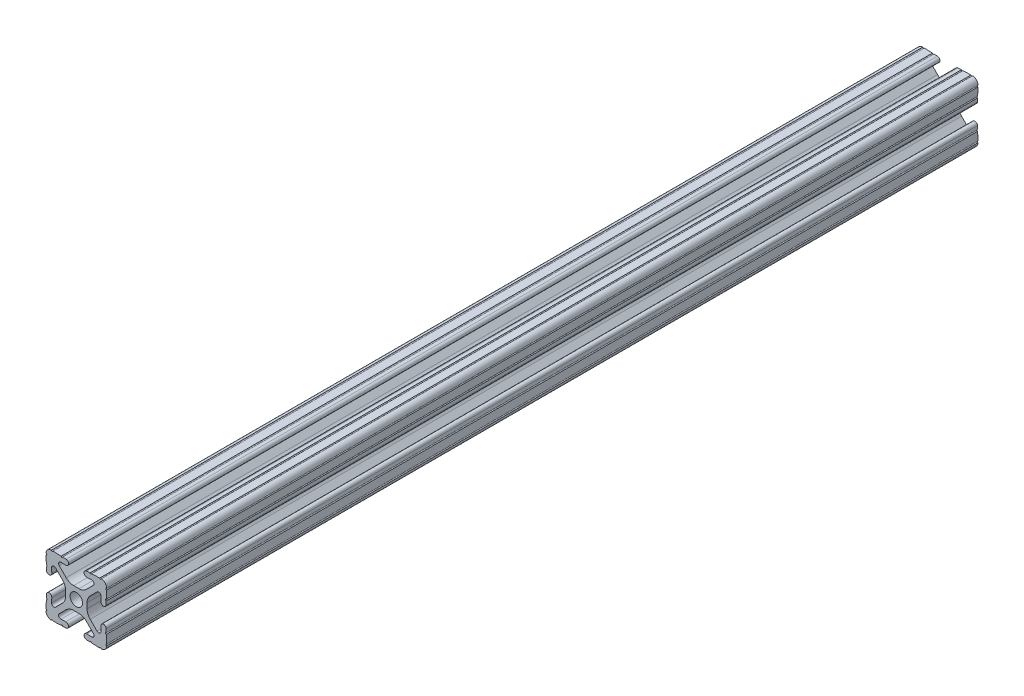
SolidWorks part; units mm, degrees
ref_plane "Front Plane" through (0, 0, 0) normal (0, 0, 1) x (1, 0, 0)
ref_plane "Top Plane" through (0, 0, 0) normal (0, 1, 0) x (1, 0, 0)
ref_plane "Right Plane" through (0, 0, 0) normal (1, 0, 0) x (0, 0, -1)
sketch "Sketch1" plane through (0, 0, 0) normal (0, 0, 1) x (1, 0, 0)
  line L0 (0, 12.7) -> (-12.7814, 12.7) construction
  line L1 (-4.5085, 0) -> (-4.5085, 2.9459)
  line L2 (-6.0437, 12.5461) -> (-10.0976, 12.6876) construction
  line L3 (-11.5616, 12.4229) -> (-4.3159, 12.1699) construction
  line L4 (-6.4364, 10.3486) -> (-6.3592, 12.5571) construction
  line L6 (-2.9459, 4.5085) -> (0, 4.5085)
  line L7 (0, 0) -> (0, 12.7) construction
  line L8 (0, 0) -> (-12.7814, 0) construction
  line L9 (0.7813, 0.7813) -> (-0.7813, -0.7813) construction
  line L10 (-2.9459, 4.5085) -> (-7.1484, 8.711)
  line L11 (-4.5085, 2.9459) -> (-8.711, 7.1484)
  line L13 (0, 0) -> (-12.7814, 12.7814) construction
  line L14 (-10.4131, 12.6987) -> (-4.3048, 12.4853)
  line L15 (-4.3048, 12.4853) -> (-4.382, 10.2769) construction
  line L16 (-4.382, 10.2769) -> (-6.4364, 10.3486)
  line L17 (-12.6987, 10.4131) -> (-12.4853, 4.3048)
  line L18 (-10.2769, 4.382) -> (-10.3486, 6.4364)
  circle A0 centre (0, 0) radius 2.6035
  arc A1 (-4.382, 10.2769) -> (-4.3048, 12.4853) centre (-4.3434, 11.3811) ccw
  arc A2 (-7.1484, 8.711) -> (-6.4364, 10.3486) centre (-6.4698, 9.3896) cw
  arc A3 (-8.711, 7.1484) -> (-10.3486, 6.4364) centre (-9.3896, 6.4698) ccw
  arc A4 (-10.2769, 4.382) -> (-12.4853, 4.3048) centre (-11.3811, 4.3434) cw
  arc A5 (-10.4131, 12.6987) -> (-12.6987, 10.4131) centre (-10.4902, 10.4902) ccw
  arc A6 (-10.4131, 12.6987) -> (-9.7821, 12.6766) centre (-10.0976, 12.6876) ccw
  arc A7 (-6.3592, 12.5571) -> (-5.7282, 12.5351) centre (-6.0437, 12.5461) ccw
  arc A8 (-12.5571, 6.3592) -> (-12.5351, 5.7282) centre (-12.5461, 6.0437) cw
  arc A9 (-12.6987, 10.4131) -> (-12.6766, 9.7821) centre (-12.6876, 10.0976) cw
  dimension "D1" = 5.207
  dimension "D5" = 14.859
  dimension "D9" = 2
  dimension "D2" = 25.4
  dimension "D12" = 0.6314
  dimension "D10" = 2.2098
  dimension "D3" = 9.017
  dimension "D4" = 9.017
  dimension "D6" = 25.4
  dimension "D7" = 6.477
  dimension "D8" = 2.2098
  dimension "D11" = 12.7
sketch "Sketch3" plane through (0, 0, 0) normal (0, 0, 1) x (1, 0, 0)
  line L0 (-2.9459, 4.5085) -> (0, 4.5085) construction
  line L1 (-2.9459, 4.5085) -> (-7.1484, 8.711) construction
  line L2 (-4.382, 10.2769) -> (-6.4364, 10.3486) construction
  line L3 (-10.4131, 12.6987) -> (-4.3048, 12.4853) construction
  line L4 (-4.5085, 0) -> (-4.5085, 2.9459) construction
  line L5 (-4.5085, 2.9459) -> (-8.711, 7.1484) construction
  line L6 (-10.2769, 4.382) -> (-10.3486, 6.4364) construction
  line L7 (-12.6987, 10.4131) -> (-12.4853, 4.3048) construction
  line L8 (-1.1153, 4.5085) -> (1.1153, 4.5085)
  line L9 (-4.2404, 5.803) -> (-7.1484, 8.711)
  line L10 (-4.382, 10.2769) -> (-6.4364, 10.3486)
  line L11 (-9.7821, 12.6766) -> (-6.3592, 12.5571)
  line L12 (-4.5085, -1.1153) -> (-4.5085, 1.1153)
  line L13 (-5.803, 4.2404) -> (-8.711, 7.1484)
  line L14 (-10.2769, 4.382) -> (-10.3486, 6.4364)
  line L15 (-12.6766, 9.7821) -> (-12.5571, 6.3592)
  line L16 (-5.7282, 12.5351) -> (-4.3048, 12.4853)
  line L17 (-12.5351, 5.7282) -> (-12.4853, 4.3048)
  line L18 (0, 0) -> (0, 12.7) construction
  line L19 (0, 0) -> (-12.7814, 0) construction
  line L20 (12.5351, 5.7282) -> (12.4853, 4.3048)
  line L21 (5.7282, 12.5351) -> (4.3048, 12.4853)
  line L22 (12.6766, 9.7821) -> (12.5571, 6.3592)
  line L23 (10.2769, 4.382) -> (10.3486, 6.4364)
  line L24 (5.803, 4.2404) -> (8.711, 7.1484)
  line L25 (4.5085, -1.1153) -> (4.5085, 1.1153)
  line L26 (9.7821, 12.6766) -> (6.3592, 12.5571)
  line L27 (4.382, 10.2769) -> (6.4364, 10.3486)
  line L28 (4.2404, 5.803) -> (7.1484, 8.711)
  line L29 (4.2404, -5.803) -> (7.1484, -8.711)
  line L30 (4.382, -10.2769) -> (6.4364, -10.3486)
  line L31 (9.7821, -12.6766) -> (6.3592, -12.5571)
  line L32 (5.803, -4.2404) -> (8.711, -7.1484)
  line L33 (10.2769, -4.382) -> (10.3486, -6.4364)
  line L34 (12.6766, -9.7821) -> (12.5571, -6.3592)
  line L35 (5.7282, -12.5351) -> (4.3048, -12.4853)
  line L36 (12.5351, -5.7282) -> (12.4853, -4.3048)
  line L37 (-12.5351, -5.7282) -> (-12.4853, -4.3048)
  line L38 (-5.7282, -12.5351) -> (-4.3048, -12.4853)
  line L39 (-12.6766, -9.7821) -> (-12.5571, -6.3592)
  line L40 (-10.2769, -4.382) -> (-10.3486, -6.4364)
  line L41 (-5.803, -4.2404) -> (-8.711, -7.1484)
  line L42 (-9.7821, -12.6766) -> (-6.3592, -12.5571)
  line L43 (-4.382, -10.2769) -> (-6.4364, -10.3486)
  line L44 (-4.2404, -5.803) -> (-7.1484, -8.711)
  line L45 (-1.1153, -4.5085) -> (1.1153, -4.5085)
  arc A0 (-10.4131, 12.6987) -> (-9.7821, 12.6766) centre (-10.0976, 12.6876) ccw construction
  arc A1 (-6.4364, 10.3486) -> (-7.1484, 8.711) centre (-6.4698, 9.3896) ccw construction
  arc A2 (-4.382, 10.2769) -> (-4.3048, 12.4853) centre (-4.3434, 11.3811) ccw construction
  arc A3 (-8.711, 7.1484) -> (-10.3486, 6.4364) centre (-9.3896, 6.4698) ccw construction
  arc A4 (-12.4853, 4.3048) -> (-10.2769, 4.382) centre (-11.3811, 4.3434) ccw construction
  arc A5 (-6.3592, 12.5571) -> (-5.7282, 12.5351) centre (-6.0437, 12.5461) ccw construction
  arc A6 (-10.4131, 12.6987) -> (-12.6987, 10.4131) centre (-10.4902, 10.4902) ccw construction
  arc A7 (-12.6766, 9.7821) -> (-12.6987, 10.4131) centre (-12.6876, 10.0976) ccw construction
  arc A8 (-12.5351, 5.7282) -> (-12.5571, 6.3592) centre (-12.5461, 6.0437) ccw construction
  arc A9 (-10.4131, 12.6987) -> (-9.7821, 12.6766) centre (-10.0976, 12.6876) ccw
  arc A10 (-6.4364, 10.3486) -> (-7.1484, 8.711) centre (-6.4698, 9.3896) ccw
  arc A11 (-4.382, 10.2769) -> (-4.3048, 12.4853) centre (-4.3434, 11.3811) ccw
  arc A12 (-8.711, 7.1484) -> (-10.3486, 6.4364) centre (-9.3896, 6.4698) ccw
  arc A13 (-12.4853, 4.3048) -> (-10.2769, 4.382) centre (-11.3811, 4.3434) ccw
  arc A14 (-6.3592, 12.5571) -> (-5.7282, 12.5351) centre (-6.0437, 12.5461) ccw
  arc A15 (-10.4131, 12.6987) -> (-12.6987, 10.4131) centre (-10.4902, 10.4902) ccw
  arc A16 (-12.6766, 9.7821) -> (-12.6987, 10.4131) centre (-12.6876, 10.0976) ccw
  arc A17 (-12.5351, 5.7282) -> (-12.5571, 6.3592) centre (-12.5461, 6.0437) ccw
  arc A18 (-1.1153, 4.5085) -> (-4.2404, 5.803) centre (-1.1153, 8.9281) cw
  arc A19 (4.5085, 1.1153) -> (5.803, 4.2404) centre (8.9281, 1.1153) cw
  arc A20 (1.1153, 4.5085) -> (4.2404, 5.803) centre (1.1153, 8.9281) ccw
  arc A21 (-4.5085, 1.1153) -> (-5.803, 4.2404) centre (-8.9281, 1.1153) ccw
  arc A22 (12.5351, 5.7282) -> (12.5571, 6.3592) centre (12.5461, 6.0437) cw
  arc A23 (12.6766, 9.7821) -> (12.6987, 10.4131) centre (12.6876, 10.0976) cw
  arc A24 (10.4131, 12.6987) -> (12.6987, 10.4131) centre (10.4902, 10.4902) cw
  arc A25 (6.3592, 12.5571) -> (5.7282, 12.5351) centre (6.0437, 12.5461) cw
  arc A26 (12.4853, 4.3048) -> (10.2769, 4.382) centre (11.3811, 4.3434) cw
  arc A27 (8.711, 7.1484) -> (10.3486, 6.4364) centre (9.3896, 6.4698) cw
  arc A28 (4.382, 10.2769) -> (4.3048, 12.4853) centre (4.3434, 11.3811) cw
  arc A29 (6.4364, 10.3486) -> (7.1484, 8.711) centre (6.4698, 9.3896) cw
  arc A30 (10.4131, 12.6987) -> (9.7821, 12.6766) centre (10.0976, 12.6876) cw
  arc A31 (10.4131, -12.6987) -> (9.7821, -12.6766) centre (10.0976, -12.6876) ccw
  arc A32 (6.4364, -10.3486) -> (7.1484, -8.711) centre (6.4698, -9.3896) ccw
  arc A33 (4.382, -10.2769) -> (4.3048, -12.4853) centre (4.3434, -11.3811) ccw
  arc A34 (8.711, -7.1484) -> (10.3486, -6.4364) centre (9.3896, -6.4698) ccw
  arc A35 (12.4853, -4.3048) -> (10.2769, -4.382) centre (11.3811, -4.3434) ccw
  arc A36 (6.3592, -12.5571) -> (5.7282, -12.5351) centre (6.0437, -12.5461) ccw
  arc A37 (10.4131, -12.6987) -> (12.6987, -10.4131) centre (10.4902, -10.4902) ccw
  arc A38 (12.6766, -9.7821) -> (12.6987, -10.4131) centre (12.6876, -10.0976) ccw
  arc A39 (12.5351, -5.7282) -> (12.5571, -6.3592) centre (12.5461, -6.0437) ccw
  arc A40 (-4.5085, -1.1153) -> (-5.803, -4.2404) centre (-8.9281, -1.1153) cw
  arc A41 (1.1153, -4.5085) -> (4.2404, -5.803) centre (1.1153, -8.9281) cw
  arc A42 (4.5085, -1.1153) -> (5.803, -4.2404) centre (8.9281, -1.1153) ccw
  arc A43 (-1.1153, -4.5085) -> (-4.2404, -5.803) centre (-1.1153, -8.9281) ccw
  arc A44 (-12.5351, -5.7282) -> (-12.5571, -6.3592) centre (-12.5461, -6.0437) cw
  arc A45 (-12.6766, -9.7821) -> (-12.6987, -10.4131) centre (-12.6876, -10.0976) cw
  arc A46 (-10.4131, -12.6987) -> (-12.6987, -10.4131) centre (-10.4902, -10.4902) cw
  arc A47 (-6.3592, -12.5571) -> (-5.7282, -12.5351) centre (-6.0437, -12.5461) cw
  arc A48 (-12.4853, -4.3048) -> (-10.2769, -4.382) centre (-11.3811, -4.3434) cw
  arc A49 (-8.711, -7.1484) -> (-10.3486, -6.4364) centre (-9.3896, -6.4698) cw
  arc A50 (-4.382, -10.2769) -> (-4.3048, -12.4853) centre (-4.3434, -11.3811) cw
  arc A51 (-6.4364, -10.3486) -> (-7.1484, -8.711) centre (-6.4698, -9.3896) cw
  arc A52 (-10.4131, -12.6987) -> (-9.7821, -12.6766) centre (-10.0976, -12.6876) cw
  circle A53 centre (0, 0) radius 2.6035 construction
  circle A54 centre (0, 0) radius 2.6035
  point P135 (4.5085, 0)
  dimension "D2" = 4.4196
extrude "Extrude1" add sketch "Sketch3" along normal mid plane 365
equation "\"D10@Sketch1\" = \"D8@Sketch1\""
equation "\"D11@Sketch1\" = \"D6@Sketch1\"/2"
equation "\"D12@Sketch1\" = \"D8@Sketch1\"/3.5"
equation "\"D2@Sketch3\" = \"D8@Sketch1\"*2"
